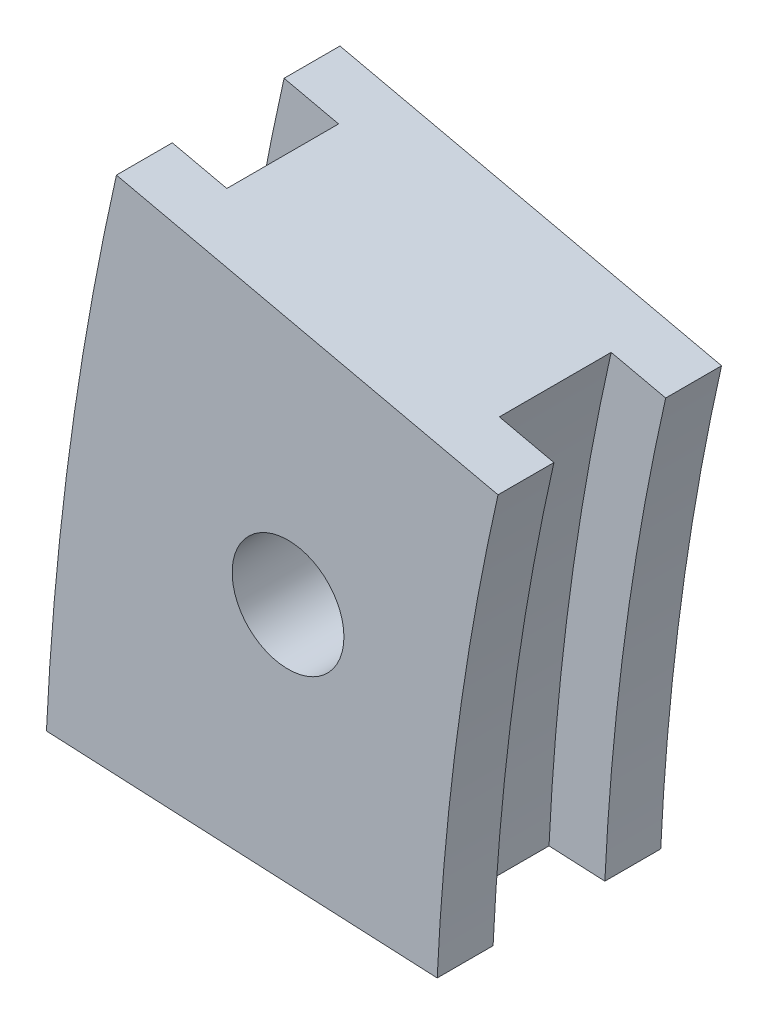
SolidWorks part; units mm, degrees
ref_plane "前视基准面" through (0, 0, 0) normal (0, 0, 1) x (1, 0, 0)
ref_plane "上视基准面" through (0, 0, 0) normal (0, 1, 0) x (1, 0, 0)
ref_plane "右视基准面" through (0, 0, 0) normal (1, 0, 0) x (0, 0, -1)
sketch "草图1" plane through (0, 0, 0) normal (0, 0, 1) x (1, 0, 0)
  line L1 (-92.8954, 4.4086) -> (-106.8797, 5.0723)
  line L2 (-90.7186, 20.4728) -> (-104.3752, 23.5547)
  arc A2 (-104.3752, 23.5547) -> (-106.8797, 5.0723) centre (0, 0) ccw
  arc A3 (-90.7186, 20.4728) -> (-92.8954, 4.4086) centre (0, 0) ccw
extrude "凸台-拉伸1" add sketch "草图1" along normal mid plane 8
sketch "草图2" plane through (0, 0, 0) normal (0, 0, 1) x (1, 0, 0)
  line L0 (-104.882, 4.9775) -> (-106.8797, 5.0723)
  line L1 (-80.0708, 18.0698) -> (-92.6695, 20.913)
  line L2 (-81.9921, 3.8912) -> (-94.8932, 4.5034)
  line L3 (-102.4242, 23.1144) -> (-104.3752, 23.5547)
  arc A1 (-104.3752, 23.5547) -> (-106.8797, 5.0723) centre (0, 0) ccw
  arc A2 (-102.4242, 23.1144) -> (-104.882, 4.9775) centre (0, 0) ccw
  arc A3 (-92.6695, 20.913) -> (-94.8932, 4.5034) centre (0, 0) ccw
  arc A4 (-80.0708, 18.0698) -> (-81.9921, 3.8912) centre (0, 0) ccw
extrude "切除-拉伸1" cut sketch "草图2" against normal blind 2 and the other way blind 2
sketch "草图3" plane through (0, 0, 4) normal (0, 0, 1) x (1, 0, 0)
  line L0 (-104.3752, 23.5547) -> (-92.8954, 4.4086)
  line L1 (-106.8797, 5.0723) -> (-90.7186, 20.4728)
  circle A0 centre (-98.2335, 13.3115) radius 2
extrude "切除-拉伸2" cut sketch "草图3" against normal through all contours L0 A0 L1 | L1 A0 L0 | L0 A0 L1 | L1 A0 L0
